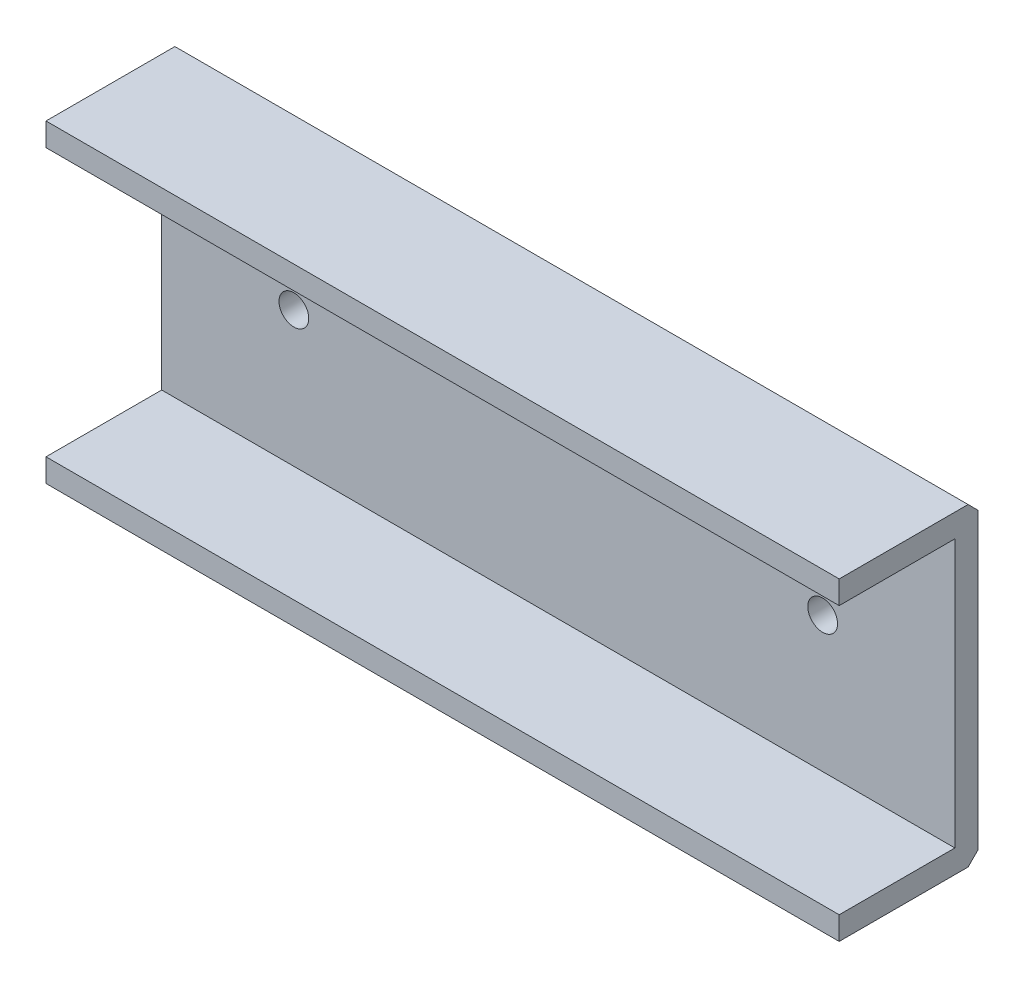
SolidWorks part; units mm, degrees
ref_plane "Alzado" through (0, 0, 0) normal (0, 0, 1) x (1, 0, 0)
ref_plane "Planta" through (0, 0, 0) normal (0, 1, 0) x (1, 0, 0)
ref_plane "Vista lateral" through (0, 0, 0) normal (1, 0, 0) x (0, 0, -1)
sketch "Croquis1" plane through (0, 0, 0) normal (1, 0, 0) x (0, 0, -1)
  line L0 (0, -23.75) -> (0, 23.75)
  line L1 (0, 23.75) -> (-21, 23.75)
  line L2 (-21, 23.75) -> (-21, 20.25)
  line L3 (-21, 20.25) -> (-3.5, 20.25)
  line L4 (-3.5, 20.25) -> (-3.5, -20.25)
  line L5 (-3.5, -20.25) -> (-21, -20.25)
  line L6 (-21, -20.25) -> (-21, -23.75)
  line L7 (-21, -23.75) -> (0, -23.75)
  point P4 (0, 0)
  dimension "D1" = 3.5
  dimension "D2" = 3.5
  dimension "D3" = 3.5
  dimension "D4" = 40.5
  dimension "D5" = 17.5
  dimension "D6" = 17.5
extrude "Saliente-Extruir1" add sketch "Croquis1" along normal mid plane 120
chamfer "Chaflán1" distance 1.5 angle 45 2 edges at (0, -23.75, 0) (0, 23.75, 0)
sketch "Croquis3" plane through (0, 0, 3.5) normal (0, 0, 1) x (1, 0, 0)
  line L0 (0, 20.25) -> (0, -20.25) construction
  line L1 (60, 20.25) -> (-60, 20.25) construction
  line L2 (60, -20.25) -> (-60, -20.25) construction
  line L3 (60, 20.25) -> (-60, 20.25) construction
  circle A0 centre (-40, 0.25) radius 2.25
  circle A1 centre (40, 0.25) radius 2.25
  dimension "D1" = 4.5
  dimension "D2" = 20
  dimension "D3" = 40
extrude "Cortar-Extruir2" cut sketch "Croquis3" against normal through all
